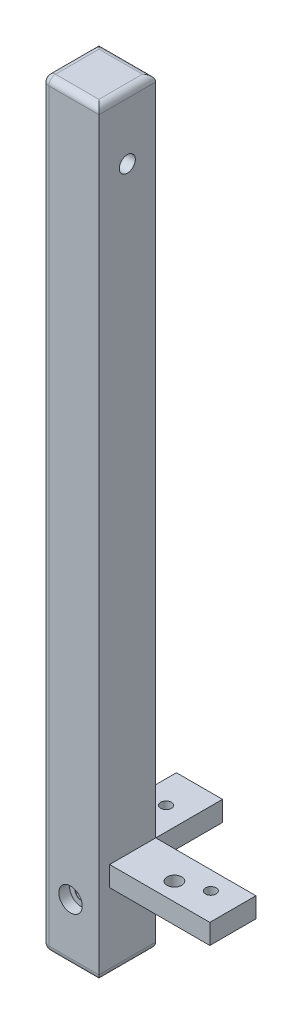
SolidWorks part; units mm, degrees
material "6061-T6 (SS)"
ref_plane "Front Plane" through (0, 0, 0) normal (0, 0, 1) x (1, 0, 0)
ref_plane "Top Plane" through (0, 0, 0) normal (0, 1, 0) x (1, 0, 0)
ref_plane "Right Plane" through (0, 0, 0) normal (1, 0, 0) x (0, 0, -1)
sketch "Sketch1" plane through (0, 0, 0) normal (0, 0, 1) x (1, 0, 0)
  line L1 (0, 0) -> (8.5, 0)
  line L2 (0, 0) -> (0, -113.5)
  line L3 (0, -113.5) -> (8.5, -113.5)
  line L4 (8.5, 0) -> (8.5, -113.5)
  dimension "D1" = 113.5
  dimension "D2" = 8.5
extrude "Boss-Extrude1" add sketch "Sketch1" along normal blind 8.5
sketch "Sketch12" plane through (8.5, 0, 0) normal (1, 0, 0) x (0, 0, -1)
  line L0 (-8.5, -113.5) -> (-8.5, 0) construction
  line L1 (-8.5, -99) -> (0, -99)
  line L2 (-8.5, -99) -> (-8.5, -102)
  line L3 (-8.5, -102) -> (0, -102)
  line L4 (0, -99) -> (0, -102)
  line L5 (0, -113.5) -> (0, 0) construction
  line L6 (-8.5, -113.5) -> (0, -113.5) construction
  dimension "D1" = 11.5
  dimension "D2" = 3
extrude "Boss-Extrude2" add sketch "Sketch12" along normal blind 15
hole_wizard "M2x0.4 Tapped Hole1" positions "Sketch14" profile "Sketch13" tap size "M2x0.4" standard "ANSI Metric"
sketch "Sketch14" plane through (0, -99, 0) normal (0, 1, 0) x (1, 0, 0)
  line L0 (0, -8.5) -> (0, 0) construction
  line L1 (23.5, -8.5) -> (8.5, -8.5) construction
  point P0 (19.5, -2.75)
  dimension "D1" = 19.5
  dimension "D2" = 5.75
sketch "Sketch13" plane through (19.5, -99, 2.75) normal (1, 0, 0) x (0, 0, 1)
  line L0 (0, 0) -> (0, 5.6807)
  line L1 (0, 5.6807) -> (0.8, 5.2)
  line L2 (0.8, 5.2) -> (0.8, 0)
  line L5 (0.8, 0) -> (0, 0)
  line L10 (0, 5.6807) -> (-0.8, 5.2) construction
  line L11 (0, -6.35) -> (0, 107.95) construction
  dimension "Tap Drill Dia." = 1.6
  dimension "Tap Drill Depth" = 5.2
  dimension "Drill Angle" = 118
cosmetic thread "Hole Thread7" parameters "D1"=3, "D2"=2
hole_wizard "Ø2.2 (2.2) Diameter Hole1" positions "Sketch16" profile "Sketch15" hole size "Ø2.2" standard "ANSI Metric"
sketch "Sketch16" plane through (0, -99, 0) normal (0, 1, 0) x (1, 0, 0)
  line L0 (23.5, -8.5) -> (8.5, -8.5) construction
  line L2 (0, -8.5) -> (0, 0) construction
  point P0 (15.5, -4.2)
  dimension "D1" = 4.3
  dimension "D2" = 15.5
sketch "Sketch15" plane through (15.5, -99, 4.2) normal (1, 0, 0) x (0, 0, 1)
  line L0 (0, 0) -> (0, 13)
  line L1 (0, 13) -> (1.1, 13)
  line L2 (1.1, 13) -> (1.1, 0)
  line L5 (1.1, 0) -> (0, 0)
  line L10 (0, 13) -> (-1.1, 13) construction
  line L11 (0, -6.35) -> (0, 107.95) construction
  dimension "Hole Dia." = 2.2
  dimension "Hole Depth" = 13
  dimension "Drill Angle" = 180
hole_wizard "CBORE for M2 Socket Head Cap Screw1" positions "Sketch20" profile "Sketch19" counterbore size "M2" standard "JIS" end condition through all
sketch "Sketch20" plane through (0, 0, 0) normal (-1, 0, 0) x (0, 0, 1)
  line L0 (8.5, 0) -> (0, 0) construction
  line L1 (0, 0) -> (0, -113.5) construction
  point P0 (4.25, -9.5)
  dimension "D1" = 9.5
  dimension "D2" = 4.25
sketch "Sketch19" plane through (0, -9.5, 4.25) normal (0, 1, 0) x (0, 0, 1)
  line L0 (0, 0) -> (0, 23.5)
  line L1 (0, 23.5) -> (1.2, 23.5)
  line L2 (1.2, 2.025) -> (1.2, 23.5)
  line L3 (1.2, 2.025) -> (1.225, 2)
  line L4 (1.225, 2) -> (2.2, 2)
  line L5 (2.2, 2) -> (2.2, 0)
  line L7 (0, 0) -> (2.2, 0)
  line L9 (-1.2, 2.025) -> (-1.225, 2) construction
  line L11 (0, -6.35) -> (0, 107.95) construction
  dimension "通し穴の直径" = 2.4
  dimension "通し穴の深さ" = 23.5
  dimension "座ぐり穴の直径" = 4.4
  dimension "座ぐり穴の深さ" = 2
  dimension "中間面の皿穴の直径" = 2.45
  dimension "中間面の皿穴の角度" = 90
sketch "Sketch25" plane through (0, 0, 0) normal (0, 0, -1) x (-1, 0, 0)
  line L0 (0, 0) -> (0, -113.5) construction
  line L1 (-8.5, -102) -> (0, -102)
  line L2 (-8.5, -102) -> (-8.5, -99)
  line L3 (-8.5, -99) -> (0, -99)
  line L4 (0, -102) -> (0, -99)
  line L6 (0, -113.5) -> (-8.5, -113.5) construction
  dimension "D1" = 3
  dimension "D2" = 11.5
extrude "Boss-Extrude3" add sketch "Sketch25" along normal blind 10
sketch "Sketch30" plane through (0, 0, 0) normal (0, 0, -1) x (-1, 0, 0)
  line L0 (-8.5, -113.5) -> (-8.5, -102) construction
  line L1 (-7, -103.5) -> (-1.5, -103.5)
  line L2 (-7, -103.5) -> (-7, -112)
  line L3 (-7, -112) -> (-1.5, -112)
  line L4 (-1.5, -103.5) -> (-1.5, -112)
  line L5 (0, -102) -> (0, -113.5) construction
  line L6 (0, -113.5) -> (-8.5, -113.5) construction
  dimension "D1" = 1.5
  dimension "D2" = 1.5
  dimension "D3" = 8.5
  dimension "D4" = 1.5
extrude "Cut-Extrude2" cut sketch "Sketch30" against normal blind 5
sketch "Sketch31" plane through (0, -113.5, 0) normal (0, -1, 0) x (-1, 0, 0)
  circle A0 centre (-4.25, -4.25) radius 1
extrude "Cut-Extrude3" cut sketch "Sketch31" against normal blind 2
fillet "Fillet1" radius 1 13 edges at (4.25, 0, 8.5) (0, -56.75, 8.5) (4.25, 0, 0) (4.25, -113.5, 0) (4.25, -113.5, 8.5) (0, 0, 4.25) (8.5, 0, 4.25) (8.5, -113.5, 4.25) (0, -113.5, 4.25) (4.25, -113.5, 3.25)
hole_wizard "M2x0.4 Tapped Hole3" positions "Sketch33" profile "Sketch32" tap size "M2x0.4" standard "ANSI Metric" end condition up to next
sketch "Sketch33" plane through (0, -99, 0) normal (0, 1, 0) x (1, 0, 0)
  line L0 (8.5, 10) -> (8.5, 0) construction
  point P0 (5.05, 5)
  dimension "D1" = 3.45
sketch "Sketch32" plane through (5.05, -99, -5) normal (1, 0, 0) x (0, 0, 1)
  line L0 (0, 0) -> (0, 3)
  line L1 (0, 3) -> (0.8, 3)
  line L2 (0.8, 3) -> (0.8, 0)
  line L5 (0.8, 0) -> (0, 0)
  line L11 (0, -6.35) -> (0, 107.95) construction
  dimension "Thru Tap Drill Dia." = 1.6
  dimension "Thru Tap Drill Depth" = 3
cosmetic thread "Hole Thread6" parameters "D2"=2
hole_wizard "M2x0.4 Tapped Hole2" positions "Sketch42" profile "Sketch41" tap size "M2x0.4" standard "ANSI Metric"
sketch "Sketch42" plane through (0, 0, 0) normal (0, 0, -1) x (-1, 0, 0)
  line L1 (0, -1) -> (0, -99) construction
  line L2 (-7.5, 0) -> (-1, 0) construction
  point P11 (-5.05, -26.8)
  point P13 (-5.05, -84.2)
  point P18 (-5.05, -31.1)
  point P20 (-5.05, -79.9)
  dimension "D1" = 5.05
  dimension "D2" = 5.05
  dimension "D3" = 4.3
  dimension "D4" = 4.3
  dimension "D5" = 26.8
sketch "Sketch41" plane through (5.05, -26.8, 0) normal (1, 0, 0) x (0, 1, 0)
  line L0 (0, 0) -> (0, 5.8009)
  line L1 (0, 5.8009) -> (1, 5.2)
  line L2 (1, 5.2) -> (1, 0)
  line L5 (1, 0) -> (0, 0)
  line L10 (0, 5.8009) -> (-1, 5.2) construction
  line L11 (0, -6.35) -> (0, 107.95) construction
  dimension "Tap Drill Dia." = 2
  dimension "Tap Drill Depth" = 5.2
  dimension "Drill Angle" = 118
cosmetic thread "Hole Thread2" parameters "D1"=4, "D2"=2
cosmetic thread "Hole Thread3" parameters "D1"=4, "D2"=2
cosmetic thread "Hole Thread4" parameters "D1"=4, "D2"=2
cosmetic thread "Hole Thread5" parameters "D1"=4, "D2"=2
hole_wizard "CBORE for M1.6 Socket Head Cap Screw1" positions "Sketch44" profile "Sketch43" counterbore size "M1.6" standard "JIS" end condition through all
sketch "Sketch44" plane through (0, 0, 8.5) normal (0, 0, 1) x (1, 0, 0)
  line L0 (8.5, -112.5) -> (8.5, -102) construction
  line L1 (7.5, -113.5) -> (1, -113.5) construction
  point P0 (4.25, -104.85)
  dimension "D1" = 4.25
  dimension "D2" = 8.65
sketch "Sketch43" plane through (4.25, -104.85, 8.5) normal (1, 0, 0) x (0, -1, 0)
  line L0 (0, 0) -> (0, 18.5)
  line L1 (0, 18.5) -> (0.9, 18.5)
  line L2 (0.9, 1.625) -> (0.9, 18.5)
  line L3 (0.9, 1.625) -> (0.925, 1.6)
  line L4 (0.925, 1.6) -> (1.75, 1.6)
  line L5 (1.75, 1.6) -> (1.75, 0)
  line L7 (0, 0) -> (1.75, 0)
  line L9 (-0.9, 1.625) -> (-0.925, 1.6) construction
  line L11 (0, -6.35) -> (0, 107.95) construction
  dimension "Thru Hole Dia." = 1.8
  dimension "Thru Hole Depth" = 18.5
  dimension "C'Bore Dia." = 3.5
  dimension "C'Bore Depth" = 1.6
  dimension "Mid C'Sink Dia." = 1.85
  dimension "Mid C'Sink Angle" = 90
sketch "Sketch45" plane through (0, -99, 0) normal (0, 1, 0) x (1, 0, 0)
  line L0 (0, 10) -> (8.5, 10) construction
  line L1 (0, 0) -> (1.6, 0)
  line L2 (0, 0) -> (0, 10)
  line L3 (0, 10) -> (1.6, 10)
  line L4 (1.6, 0) -> (1.6, 10)
  line L5 (23.5, 0) -> (23.5, -8.5) construction
  line L6 (8.5, -8.5) -> (23.5, -8.5)
  line L7 (8.5, -8.5) -> (8.5, -6.9)
  line L8 (8.5, -6.9) -> (23.5, -6.9)
  line L9 (23.5, -8.5) -> (23.5, -6.9)
  dimension "D1" = 1.6
  dimension "D2" = 1.6
extrude "Cut-Extrude4" cut sketch "Sketch45" against normal blind 10
